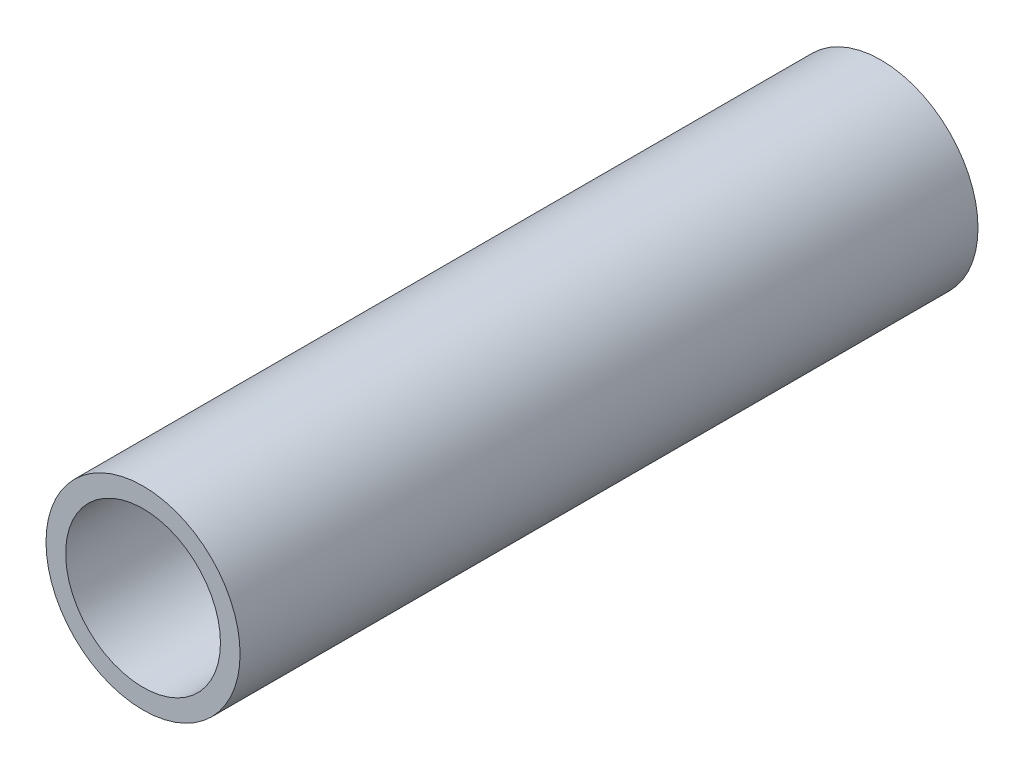
SolidWorks part; units mm, degrees
ref_plane "Front Plane" through (0, 0, 0) normal (0, 0, 1) x (1, 0, 0)
ref_plane "Top Plane" through (0, 0, 0) normal (0, 1, 0) x (1, 0, 0)
ref_plane "Right Plane" through (0, 0, 0) normal (1, 0, 0) x (0, 0, -1)
sketch "Sketch1" plane through (0, 0, 0) normal (0, 0, 1) x (1, 0, 0)
  circle A0 centre (0, 0) radius 16.7005
  dimension "Pipe OD" = 33.401
extrude "Extrude-Thin1" add sketch "Sketch1" along normal mid plane 127 thin thin type one direction reverse wall 3.3782
